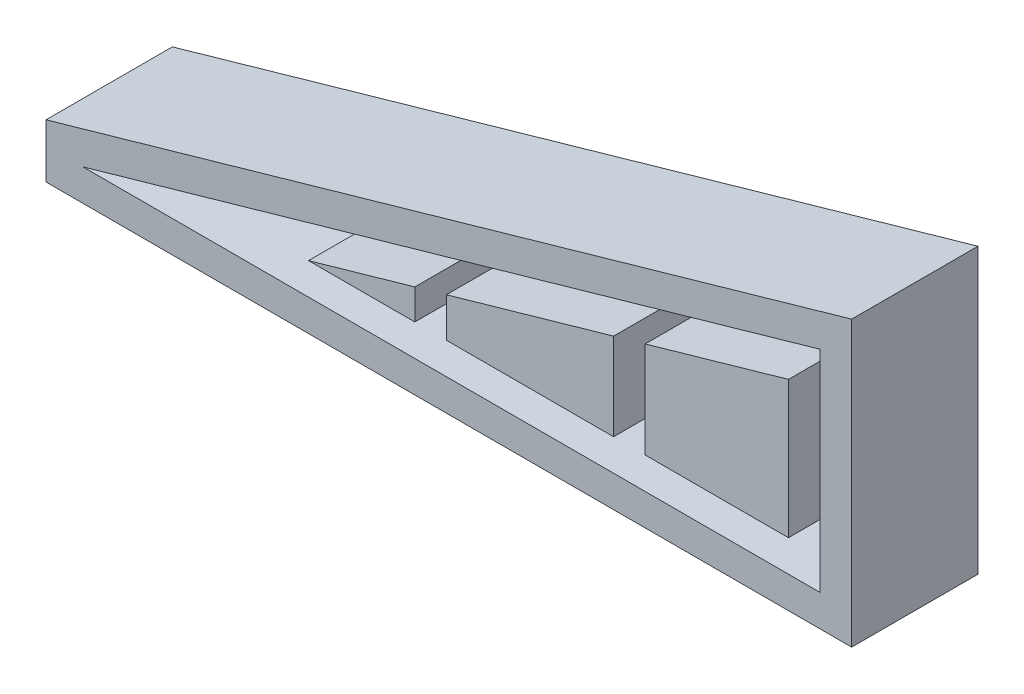
SolidWorks part; units mm, degrees
ref_plane "Front Plane" through (0, 0, 0) normal (0, 0, 1) x (1, 0, 0)
ref_plane "Top Plane" through (0, 0, 0) normal (0, 1, 0) x (1, 0, 0)
ref_plane "Right Plane" through (0, 0, 0) normal (1, 0, 0) x (0, 0, -1)
sketch "Sketch1" plane through (0, 0, 0) normal (0, 0, 1) x (1, 0, 0)
  line L0 (28.48, 5.5859) -> (28.48, -14.4141)
  line L1 (28.48, -14.4141) -> (-41.52, -14.4141)
  line L2 (-41.52, -14.4141) -> (28.48, 5.5859)
  line L3 (25.48, 1.6087) -> (25.48, -11.4141)
  line L4 (25.48, -11.4141) -> (11.8727, -11.4141)
  line L5 (11.8727, -11.4141) -> (11.8727, -2.2792)
  line L6 (11.8727, -2.2792) -> (25.48, 1.6087)
  line L7 (8.8727, -3.1363) -> (8.8727, -11.4141)
  line L8 (8.8727, -11.4141) -> (-7.0056, -11.4141)
  line L9 (-7.0056, -11.4141) -> (-7.0056, -7.6729)
  line L10 (-7.0056, -7.6729) -> (8.8727, -3.1363)
  line L11 (-10.0056, -8.5301) -> (-10.0056, -11.4141)
  line L12 (-10.0056, -11.4141) -> (-20.0998, -11.4141)
  line L13 (-20.0998, -11.4141) -> (-10.0056, -8.5301)
  line L14 (11.8727, -2.2792) -> (8.8727, -3.1363) construction
  line L15 (-7.0056, -7.6729) -> (-10.0056, -8.5301) construction
  line L16 (-10.0056, -11.4141) -> (-7.0056, -11.4141) construction
  line L17 (8.8727, -11.4141) -> (11.8727, -11.4141) construction
  line L18 (-45.0297, -12.2969) -> (31.48, 9.563)
  line L19 (31.48, 9.563) -> (31.48, -17.4141)
  line L20 (31.48, -17.4141) -> (-45.0297, -17.4141)
  line L21 (-45.0297, -17.4141) -> (-45.0297, -12.2969)
  point P13 (-10.0056, -9.9721)
  dimension "D1" = 70
  dimension "D2" = 20
  dimension "D3" = 3
  dimension "D4" = 3
  dimension "D5" = 3
  dimension "D6" = 3
  dimension "D7" = 3
  dimension "D8" = 3
  dimension "D9" = 3
  dimension "D10" = 3
extrude "Boss-Extrude1" add sketch "Sketch1" along normal blind 10 contours L21 L20 L19 L18 L1 L2 L0 | L13 L12 L11 | L10 L9 L8 L7 | L6 L5 L4 L3
sketch "Sketch2" plane through (0, 0, 0) normal (0, 0, -1) x (-1, 0, 0)
  line L0 (-31.48, 9.563) -> (45.0297, -12.2969)
  line L1 (45.0297, -12.2969) -> (45.0297, -17.4141)
  line L2 (45.0297, -17.4141) -> (-31.48, -17.4141)
  line L3 (-31.48, -17.4141) -> (-31.48, 9.563)
extrude "Boss-Extrude2" add sketch "Sketch2" along normal blind 2
